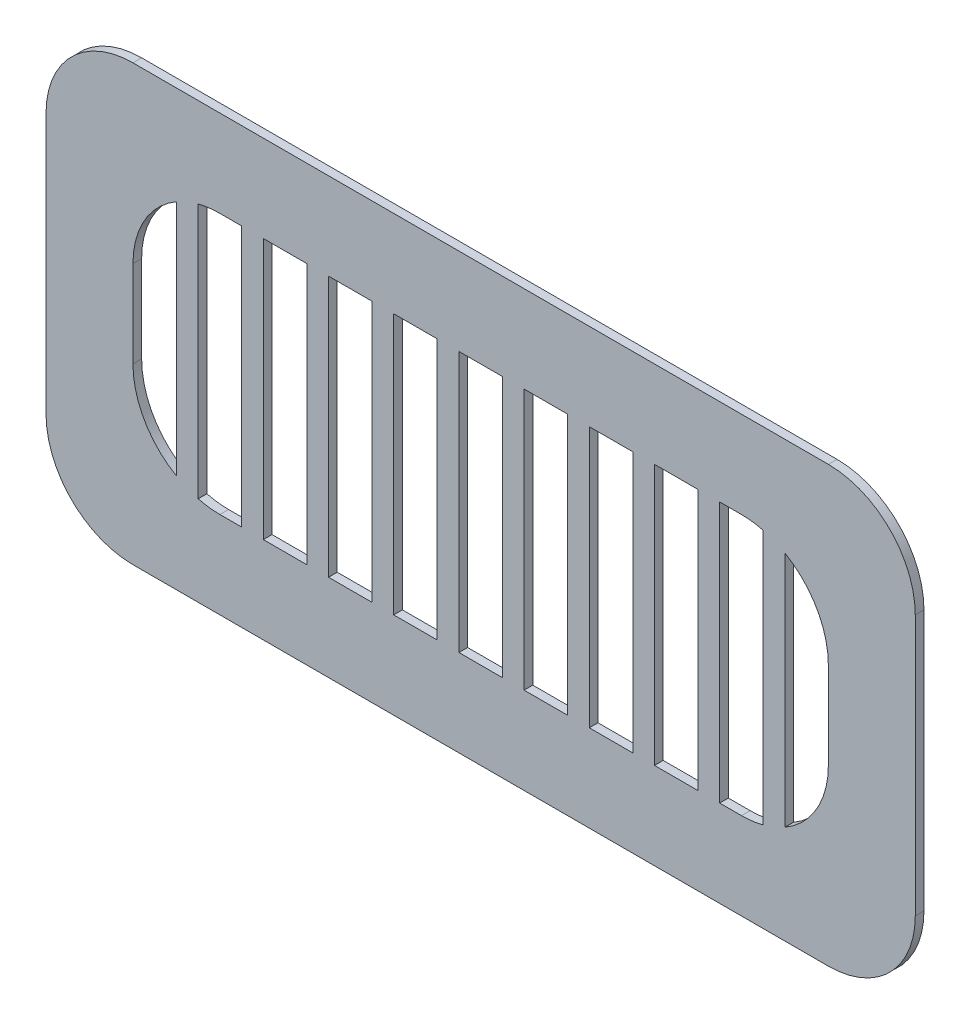
SolidWorks part; units mm, degrees
ref_plane "Front Plane" through (0, 0, 0) normal (0, 0, 1) x (1, 0, 0)
ref_plane "Top Plane" through (0, 0, 0) normal (0, 1, 0) x (1, 0, 0)
ref_plane "Right Plane" through (0, 0, 0) normal (1, 0, 0) x (0, 0, -1)
sketch "Sketch1" plane through (0, 0, 0) normal (0, 0, 1) x (1, 0, 0)
  line L0 (-50, 0) -> (50, 0) construction
  line L1 (-40, 25) -> (40, 25)
  line L2 (-50, 15) -> (-50, -15)
  line L3 (-40, -25) -> (40, -25)
  line L4 (50, 15) -> (50, -15)
  line L5 (0, 25) -> (0, -25) construction
  line L7 (-30, 15) -> (30, 15)
  line L8 (-40, 5) -> (-40, -5)
  line L9 (-30, -15) -> (30, -15)
  line L10 (40, 5) -> (40, -5)
  arc A0 (40, -25) -> (50, -15) centre (40, -15) ccw
  arc A1 (-50, -15) -> (-40, -25) centre (-40, -15) ccw
  arc A2 (40, 25) -> (50, 15) centre (40, 15) cw
  arc A3 (-40, 25) -> (-50, 15) centre (-40, 15) ccw
  arc A4 (-30, -15) -> (-40, -5) centre (-30, -5) cw
  arc A5 (30, -15) -> (40, -5) centre (30, -5) ccw
  arc A6 (30, 15) -> (40, 5) centre (30, 5) cw
  arc A7 (-30, 15) -> (-40, 5) centre (-30, 5) ccw
  dimension "D3" = 10
  dimension "D8" = 10
  dimension "D2" = 50
  dimension "D4" = 10
  dimension "D5" = 10
  dimension "D6" = 10
  dimension "D7" = 10
extrude "Boss-Extrude1" add sketch "Sketch1" along normal blind 1
sketch "Sketch3" plane through (0, 0, 1) normal (0, 0, 1) x (1, 0, 0)
  line L0 (30, 15) -> (-30, 15) construction
  line L1 (-35, 15) -> (-32.5, 15)
  line L2 (-35, 15) -> (-35, -15)
  line L3 (-35, -15) -> (-32.5, -15)
  line L4 (-32.5, 15) -> (-32.5, -15)
  line L5 (-30, -15) -> (30, -15) construction
  line L6 (-40, 5) -> (-40, -5) construction
  line L7 (-27.5, 15) -> (-27.5, -15)
  line L8 (-27.5, 15) -> (-25, 15)
  line L9 (-25, 15) -> (-25, -15)
  line L10 (-27.5, -15) -> (-25, -15)
  line L11 (-20, 15) -> (-20, -15)
  line L12 (-20, 15) -> (-17.5, 15)
  line L13 (-17.5, 15) -> (-17.5, -15)
  line L14 (-20, -15) -> (-17.5, -15)
  line L15 (-12.5, 15) -> (-12.5, -15)
  line L16 (-12.5, 15) -> (-10, 15)
  line L17 (-10, 15) -> (-10, -15)
  line L18 (-12.5, -15) -> (-10, -15)
  line L19 (-5, 15) -> (-5, -15)
  line L20 (-5, 15) -> (-2.5, 15)
  line L21 (-2.5, 15) -> (-2.5, -15)
  line L22 (-5, -15) -> (-2.5, -15)
  line L23 (2.5, 15) -> (2.5, -15)
  line L24 (2.5, 15) -> (5, 15)
  line L25 (5, 15) -> (5, -15)
  line L26 (2.5, -15) -> (5, -15)
  line L27 (10, 15) -> (10, -15)
  line L28 (10, 15) -> (12.5, 15)
  line L29 (12.5, 15) -> (12.5, -15)
  line L30 (10, -15) -> (12.5, -15)
  line L31 (17.5, 15) -> (17.5, -15)
  line L32 (17.5, 15) -> (20, 15)
  line L33 (20, 15) -> (20, -15)
  line L34 (17.5, -15) -> (20, -15)
  line L35 (25, 15) -> (25, -15)
  line L36 (25, 15) -> (27.5, 15)
  line L37 (27.5, 15) -> (27.5, -15)
  line L38 (25, -15) -> (27.5, -15)
  line L39 (32.5, 15) -> (32.5, -15)
  line L40 (32.5, 15) -> (35, 15)
  line L41 (35, 15) -> (35, -15)
  line L42 (32.5, -15) -> (35, -15)
  dimension "D1" = 5
  dimension "D2" = 2.5
extrude "Boss-Extrude2" add sketch "Sketch3" against normal blind 1
